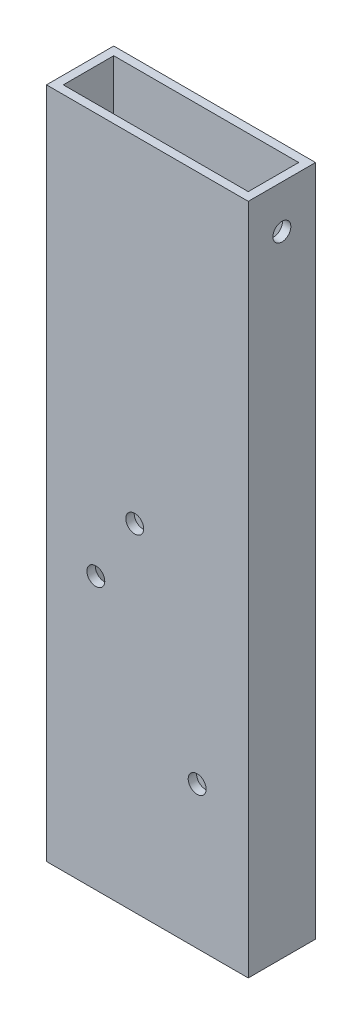
SolidWorks part; units mm, degrees
material "6061-T6 (SS)"
ref_plane "Front Plane" through (0, 0, 0) normal (0, 0, 1) x (1, 0, 0)
ref_plane "Top Plane" through (0, 0, 0) normal (0, 1, 0) x (1, 0, 0)
ref_plane "Right Plane" through (0, 0, 0) normal (1, 0, 0) x (0, 0, -1)
sketch "Sketch1" plane through (0, 0, 0) normal (0, 1, 0) x (1, 0, 0)
  line L0 (3.175, 22.225) -> (73.025, 22.225)
  line L1 (0, 0) -> (76.2, 0)
  line L2 (0, 0) -> (0, 25.4)
  line L3 (0, 25.4) -> (76.2, 25.4)
  line L4 (76.2, 0) -> (76.2, 25.4)
  line L5 (73.025, 3.175) -> (73.025, 22.225)
  line L6 (3.175, 3.175) -> (73.025, 3.175)
  line L7 (3.175, 3.175) -> (3.175, 22.225)
  dimension "D1" = 76.2
  dimension "D2" = 25.4
  dimension "D3" = 3.175
extrude "Boss-Extrude1" add sketch "Sketch1" along normal blind 254
sketch "Sketch3" plane through (0, 0, 0) normal (0, 0, 1) x (1, 0, 0)
  circle A0 centre (56.8977, 53.7837) radius 3.3782
  circle A1 centre (18.6364, 102.6382) radius 3.3782
  circle A2 centre (33.3306, 127.1456) radius 3.3782
  dimension "D1" = 6.7564
  dimension "D2" = 6.7564
  dimension "D3" = 6.7564
extrude "Cut-Extrude1" cut sketch "Sketch3" against normal through all
sketch "Sketch4" plane through (0, 0, 0) normal (-1, 0, 0) x (0, 0, 1)
  circle A0 centre (-12.7, 237.7313) radius 3.3782
  dimension "D1" = 6.7564
extrude "Cut-Extrude2" cut sketch "Sketch4" against normal through all and the other way through all
